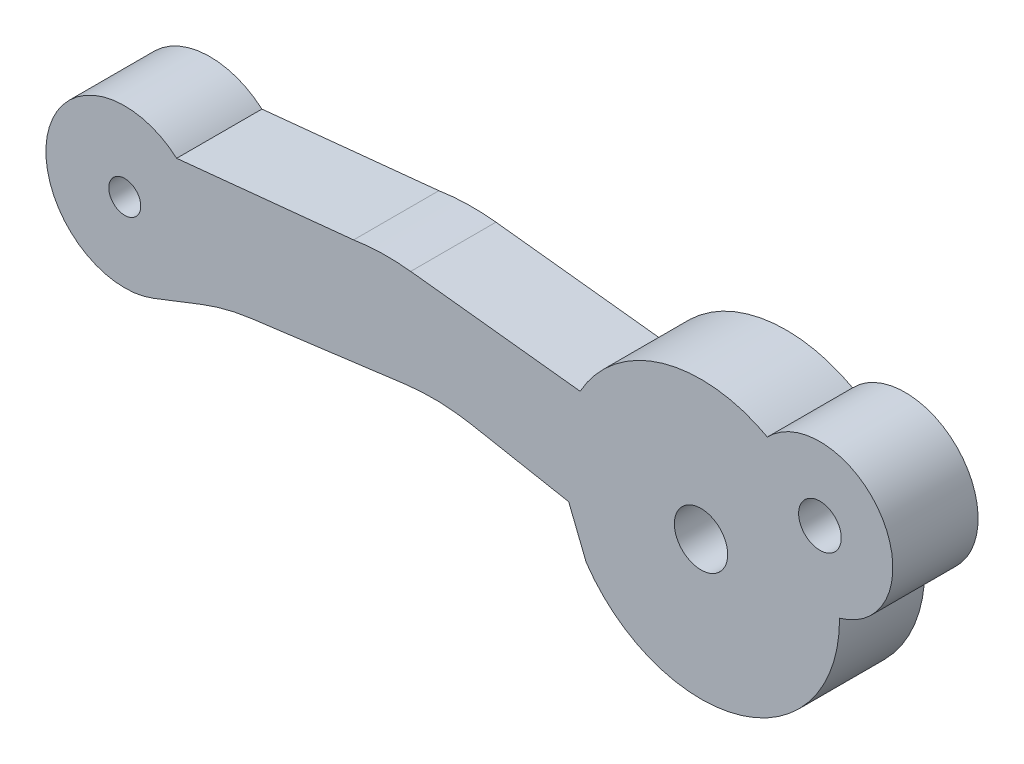
SolidWorks part; units mm, degrees
ref_plane "Front Plane" through (0, 0, 0) normal (0, 0, 1) x (1, 0, 0)
ref_plane "Top Plane" through (0, 0, 0) normal (0, 1, 0) x (1, 0, 0)
ref_plane "Right Plane" through (0, 0, 0) normal (1, 0, 0) x (0, 0, -1)
sketch "Sketch1" plane through (0, 0, 0) normal (0, 0, 1) x (1, 0, 0)
  line L0 (18.4058, -9.3761) -> (25.6286, -8.4354)
  line L1 (33.8349, -4.619) -> (25.8852, -3.7235)
  line L3 (13.8131, -10.8528) -> (16.0665, -9.9747)
  line L9 (33.299, -9.3761) -> (34.1209, -11.4306)
  line L10 (23.208, -3.7827) -> (14.9043, -4.619)
  line L11 (28.7684, -8.524) -> (33.299, -9.3761)
  arc A0 (46.0074, -7.752) -> (42.6202, -2.0864) centre (45.0865, -4.4573) ccw
  arc A1 (34.1209, -11.4306) -> (46.0074, -7.752) centre (39.5075, -7.7926) ccw
  arc A2 (14.9043, -4.619) -> (13.8131, -10.8528) centre (12.4697, -7.4053) ccw
  arc A3 (42.6202, -2.0864) -> (33.8349, -4.619) centre (39.5075, -7.7926) ccw
  arc A4 (25.8852, -3.7235) -> (23.208, -3.7827) centre (24.7657, -13.6606) ccw
  circle A9 centre (12.4697, -7.4053) radius 0.75
  circle A10 centre (39.5075, -7.7926) radius 1.25
  circle A11 centre (45.0865, -4.4573) radius 1
  arc A12 (16.0665, -9.9747) -> (18.4058, -9.3761) centre (19.6972, -19.2923) cw
  arc A14 (25.6286, -8.4354) -> (28.7684, -8.524) centre (26.9201, -18.3517) cw
  dimension "D1" = 10
  dimension "D2" = 10
  dimension "D3" = 10
  dimension "D4" = 1.5
  dimension "D5" = 6.5
  dimension "D6" = 3.7
  dimension "D8" = 2.5
  dimension "D9" = 2
  dimension "D10" = 8
extrude "Boss-Extrude2" add sketch "Sketch1" along normal blind 4
